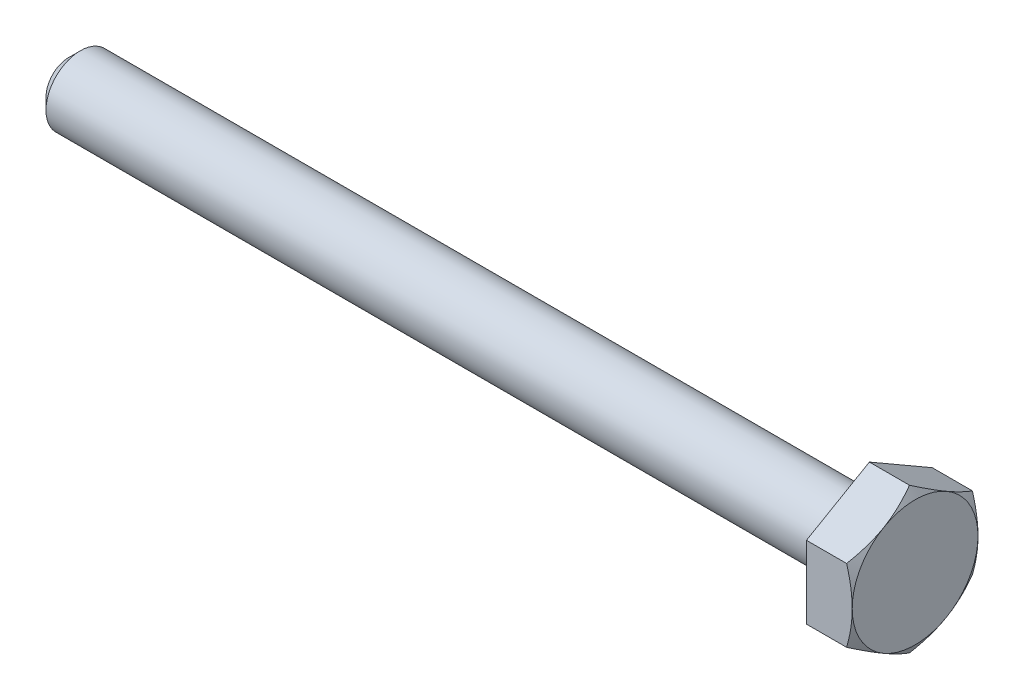
SolidWorks part; units mm, degrees
material "Stal węglowa"
ref_plane "Płaszczyzna XY" through (0, 0, 0) normal (0, 0, 1) x (1, 0, 0)
ref_plane "Płaszczyzna XZ" through (0, 0, 0) normal (0, 1, 0) x (1, 0, 0)
ref_plane "Płaszczyzna YZ" through (0, 0, 0) normal (1, 0, 0) x (0, 0, -1)
sketch "Szkic1" plane through (0, 0, 0) normal (0, 0, 1) x (1, 0, 0)
  line L0 (-37, 0) -> (0, 0) construction
  line L1 (0, 0) -> (0, 2.75)
  line L2 (0, 2.75) -> (-2, 2.75)
  line L3 (-2, 2.75) -> (-2, 1.5)
  line L4 (-2, 1.5) -> (-37, 1.5)
  line L5 (-37, 1.5) -> (-37, 0)
  line L6 (-37, 0) -> (0, 0)
  point P3 (-1, 2.75)
  dimension "sw" = 5.5
  dimension "d" = 3
  dimension "l" = 35
  dimension "k" = 2
revolve "Obrót1" add sketch "Szkic1" angle 360 about L0
sketch "Szkic2" plane through (0, 0, 0) normal (1, 0, 0) x (0, 0, -1)
  line L1 (-2.75, 1.5877) -> (-2.75, -1.5877)
  line L2 (-2.75, -1.5877) -> (0, -3.1754)
  line L3 (0, -3.1754) -> (2.75, -1.5877)
  line L4 (2.75, -1.5877) -> (2.75, 1.5877)
  line L5 (2.75, 1.5877) -> (0, 3.1754)
  line L6 (0, 3.1754) -> (-2.75, 1.5877)
  circle A0 centre (0, 0) radius 2.75 construction
  circle A1 centre (0, 0) radius 2.75 construction
extrude "Dodanie-wyciągnięcie1" add sketch "Szkic2" against normal up to surface (2 mm away) up to face at (-2, 0, 1.5)
chamfer "Sfazowanie1" distance 0.5 angle 45 1 edges at (-37, 0, 1.5)
sketch "Szkic9" plane through (0, 0, 0) normal (0, 0, 1) x (1, 0, 0)
  line L0 (0, 3.1754) -> (0, 2.75)
  line L4 (0, 2.75) -> (-2, 2.75) construction
  line L5 (0, 2.75) -> (-0.2456, 3.1754)
  line L6 (-2, 3.1754) -> (0, 3.1754) construction
  line L7 (-0.2456, 3.1754) -> (0, 3.1754)
  line L8 (-1, 0) -> (-1, 3.1754) construction
  line L9 (-37, 0) -> (0, 0) construction
  line L10 (0, 0) -> (-2.2665, 0) construction
  dimension "D1" = 30
revolve "Wycięcie-obrót1" cut sketch "Szkic9" angle 360 about L6
